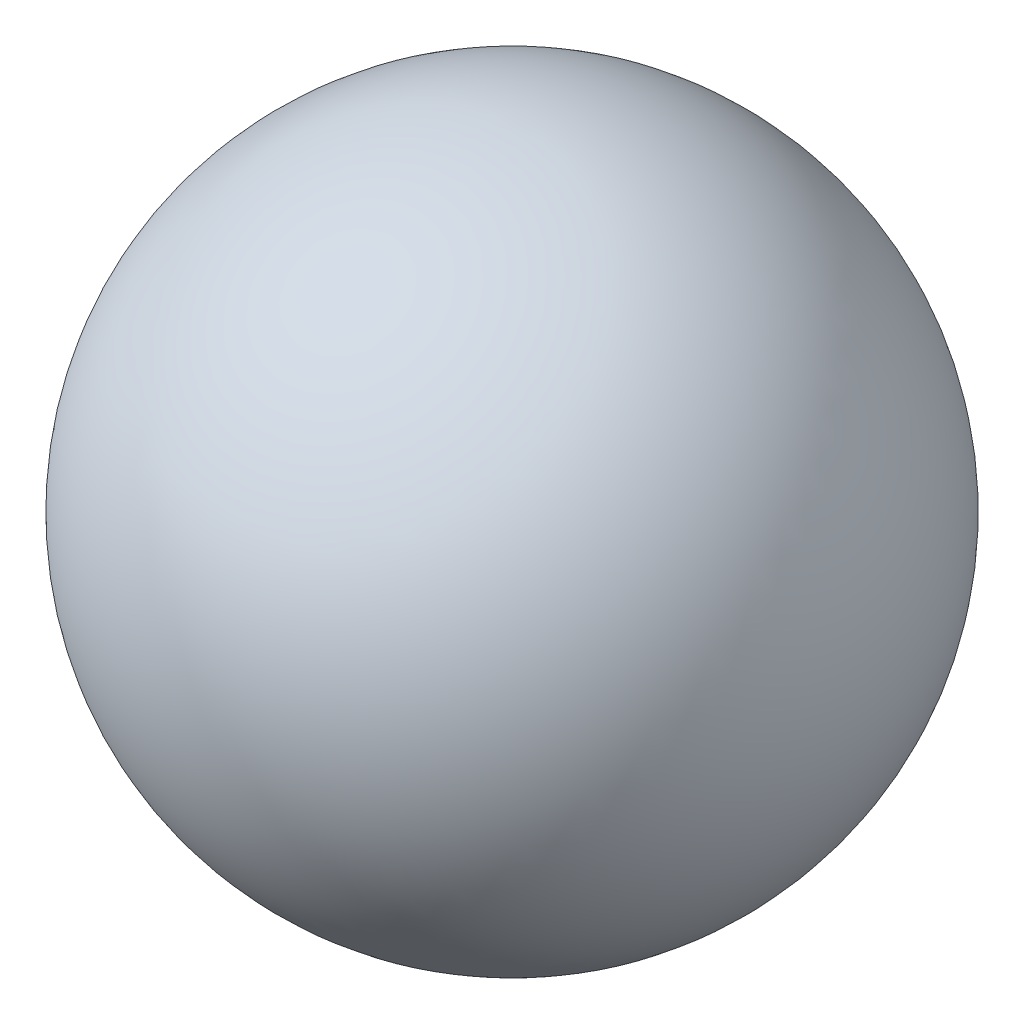
SolidWorks part; units mm, degrees
ref_plane "Plan de face" through (0, 0, 0) normal (0, 0, 1) x (1, 0, 0)
ref_plane "Plan de dessus" through (0, 0, 0) normal (0, 1, 0) x (1, 0, 0)
ref_plane "Plan de droite" through (0, 0, 0) normal (1, 0, 0) x (0, 0, -1)
sketch "Esquisse1" plane through (0, 0, 0) normal (0, 0, 1) x (1, 0, 0)
  line L0 (0, 30) -> (0, -30)
  line L1 (0, 60.1744) -> (0, -48.4884) construction
  arc A0 (0, 30) -> (0, -30) centre (0, 0) cw
  dimension "D1" = 30
revolve "Révolution1" add sketch "Esquisse1" angle 360 about L1
